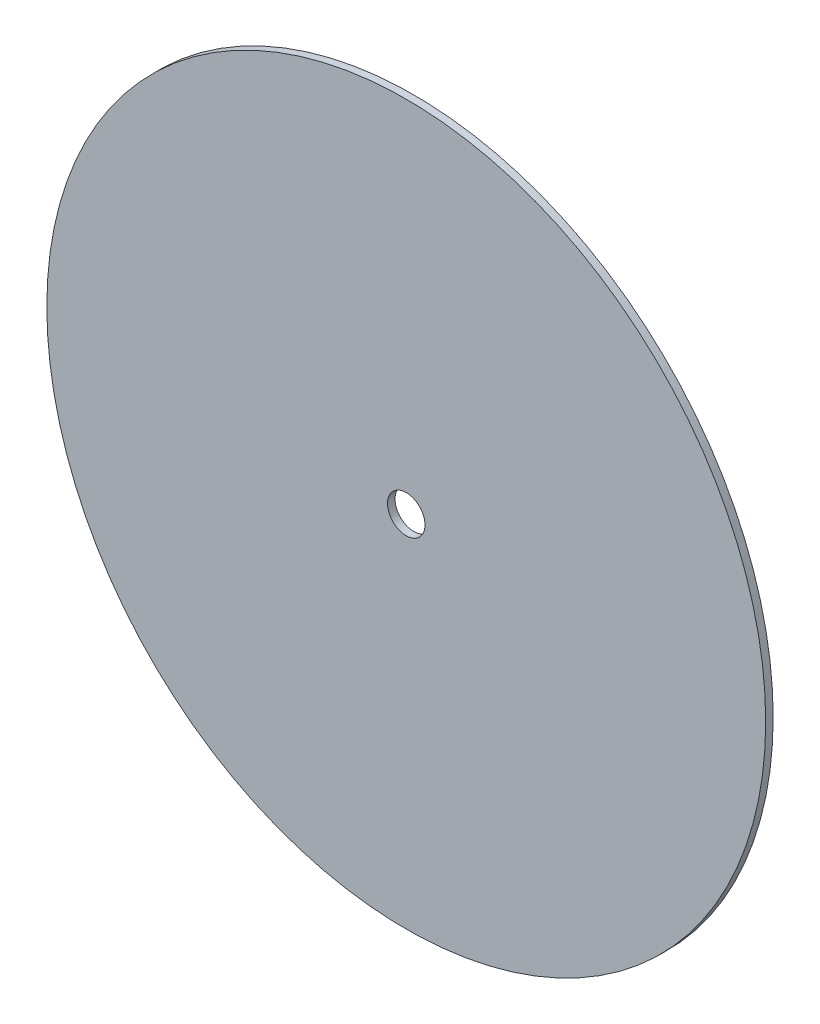
SolidWorks part; units mm, degrees
material "Cast Carbon Steel"
ref_plane "Front Plane" through (0, 0, 0) normal (0, 0, 1) x (1, 0, 0)
ref_plane "Top Plane" through (0, 0, 0) normal (0, 1, 0) x (1, 0, 0)
ref_plane "Right Plane" through (0, 0, 0) normal (1, 0, 0) x (0, 0, -1)
sketch "Sketch1" plane through (0, 0, 0) normal (0, 0, 1) x (1, 0, 0)
  circle A0 centre (0, 0) radius 7.9375
  circle A1 centre (0, 0) radius 152.4
  dimension "D1" = 15.875
  dimension "D2" = 304.8
extrude "Boss-Extrude1" add sketch "Sketch1" along normal mid plane 3.175
